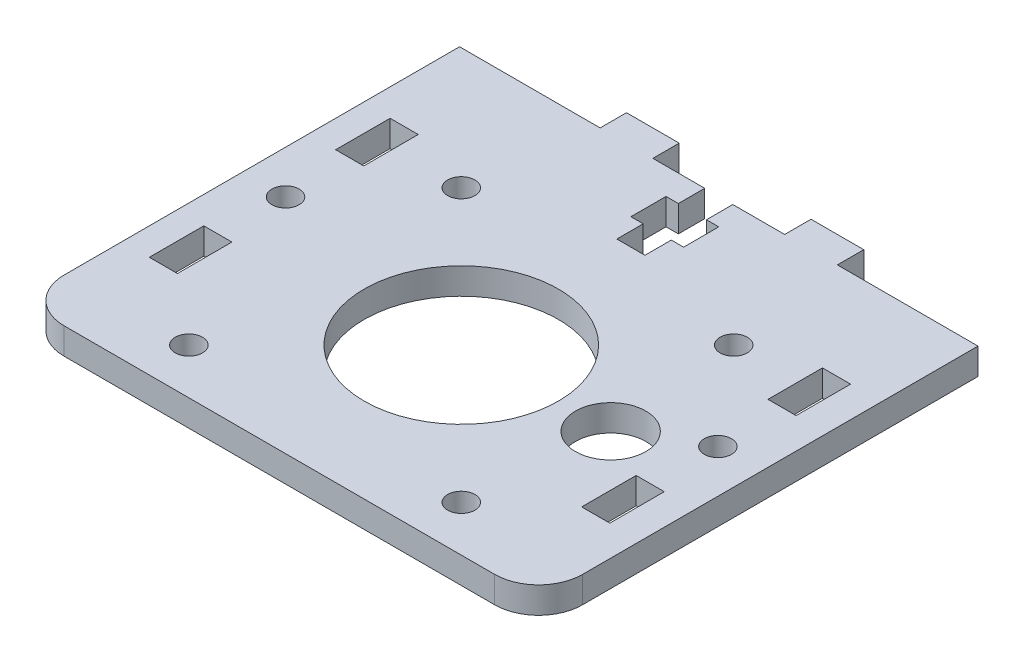
SolidWorks part; units mm, degrees
ref_plane "Alzado" through (0, 0, 0) normal (0, 0, 1) x (1, 0, 0)
ref_plane "Planta" through (0, 0, 0) normal (0, 1, 0) x (1, 0, 0)
ref_plane "Vista lateral" through (0, 0, 0) normal (1, 0, 0) x (0, 0, -1)
sketch "Croquis1" plane through (0, 0, 0) normal (0, 1, 0) x (1, 0, 0)
  line L0 (59, 50) -> (0, 0) construction
  line L1 (5, 0) -> (54, 0)
  line L2 (0, 5) -> (0, 50)
  line L3 (0, 50) -> (16, 50)
  line L4 (59, 5) -> (59, 50)
  line L5 (31.1, 50) -> (37, 50)
  line L7 (16, 50) -> (16, 53)
  line L8 (16, 53) -> (22, 53)
  line L9 (22, 50) -> (22, 53)
  line L11 (37, 50) -> (37, 53)
  line L12 (37, 53) -> (43, 53)
  line L13 (43, 50) -> (43, 53)
  line L15 (27.9, 50) -> (27.9, 47)
  line L16 (27.9, 40) -> (31.1, 40)
  line L17 (31.1, 50) -> (31.1, 47)
  line L18 (26.5, 47) -> (27.9, 47)
  line L19 (26.5, 47) -> (26.5, 43)
  line L20 (26.5, 43) -> (27.9, 43)
  line L21 (32.5, 47) -> (32.5, 43)
  line L22 (31.1, 47) -> (32.5, 47)
  line L23 (31.1, 43) -> (31.1, 40)
  line L24 (27.9, 43) -> (27.9, 40)
  line L25 (31.1, 43) -> (32.5, 43)
  line L26 (22, 50) -> (27.9, 50)
  line L27 (43, 50) -> (59, 50)
  line L28 (29.5, 40) -> (29.5, 0.0002) construction
  line L29 (3.1, 17.8) -> (6.3, 17.8)
  line L30 (3.1, 17.8) -> (3.1, 11.6)
  line L31 (3.1, 11.6) -> (6.3, 11.6)
  line L32 (6.3, 17.8) -> (6.3, 11.6)
  line L33 (3.1, 39) -> (6.3, 39)
  line L34 (3.1, 39) -> (3.1, 32.8)
  line L35 (3.1, 32.8) -> (6.3, 32.8)
  line L36 (6.3, 39) -> (6.3, 32.8)
  line L58 (29.5, 20.7) -> (59, 20.7) construction
  line L59 (29.5, 20.7) -> (0, 20.7) construction
  line L76 (55.5, 39) -> (55.5, 32.8)
  line L77 (52.3, 39) -> (55.5, 39)
  line L78 (52.3, 39) -> (52.3, 32.8)
  line L79 (52.3, 32.8) -> (55.5, 32.8)
  line L80 (55.5, 17.8) -> (55.5, 11.6)
  line L81 (52.3, 17.8) -> (55.5, 17.8)
  line L82 (52.3, 17.8) -> (52.3, 11.6)
  line L83 (52.3, 11.6) -> (55.5, 11.6)
  circle A1 centre (4.9, 25.3) radius 1.55
  circle A4 centre (29.5, 20.7) radius 11.05
  circle A5 centre (14, 36.2) radius 1.55
  circle A6 centre (45, 36.2) radius 1.55
  circle A7 centre (45, 5.2) radius 1.55
  circle A8 centre (14, 5.2) radius 1.55
  circle A9 centre (46.5, 20.7) radius 4
  arc A10 (54, 0) -> (59, 5) centre (54, 5) ccw
  arc A11 (5, 0) -> (0, 5) centre (5, 5) cw
  circle A14 centre (54.1, 25.3) radius 1.55
  point P5 (29.5, 25)
  point P54 (29.5, 20.7)
  point P65 (59, 0)
  dimension "D3" = 22.1
  dimension "D25" = 3.1
  dimension "D26" = 7.5
  dimension "D28" = 20.7
  dimension "D29" = 31
  dimension "D33" = 15.5
  dimension "D34" = 15.5
  dimension "D31" = 3.1
  dimension "D32" = 3.1
  dimension "D35" = 8
  dimension "D37" = 5
  dimension "D1" = 59
  dimension "D2" = 50
  dimension "D4" = 6
  dimension "D5" = 3
  dimension "D6" = 6
  dimension "D7" = 3
  dimension "D8" = 15
  dimension "D9" = 16
  dimension "D10" = 10
  dimension "D11" = 3.2
  dimension "D12" = 5.9
  dimension "D13" = 4
  dimension "D14" = 6
  dimension "D15" = 3
  dimension "D16" = 1.4
  dimension "D17" = 6.2
  dimension "D18" = 3.2
  dimension "D19" = 6.2
  dimension "D20" = 3.2
  dimension "D21" = 15
  dimension "D22" = 3.1
  dimension "D23" = 3.1
  dimension "D24" = 11.6
  dimension "D27" = 4.9
  dimension "D30" = 15.5
  dimension "D36" = 17
  dimension "D39" = 46
  dimension "D38" = 2
extrude "Saliente-Extruir1" add sketch "Croquis1" along normal blind 3
